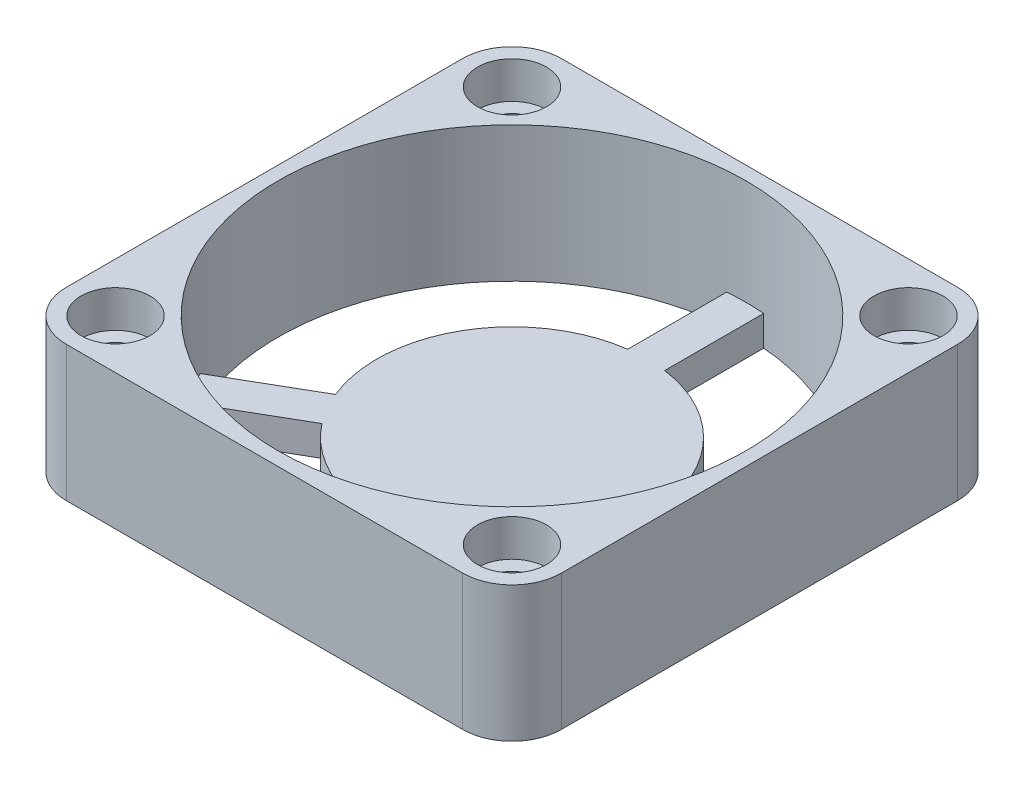
SolidWorks part; units mm, degrees
ref_plane "Plano frontal" through (0, 0, 0) normal (0, 0, 1) x (1, 0, 0)
ref_plane "Plano superior" through (0, 0, 0) normal (0, 1, 0) x (1, 0, 0)
ref_plane "Plano direito" through (0, 0, 0) normal (1, 0, 0) x (0, 0, -1)
sketch "Esboço1" plane through (0, 0, 0) normal (0, 1, 0) x (1, 0, 0)
  line L1 (-16.1, -20.1) -> (16.1, -20.1)
  line L2 (-20.1, -16.1) -> (-20.1, 16.1)
  line L3 (-16.1, 20.1) -> (16.1, 20.1)
  line L4 (20.1, -16.1) -> (20.1, 16.1)
  line L5 (0, 20.1) -> (0, -20.1) construction
  line L6 (-20.1, 0) -> (20.1, 0) construction
  arc A0 (16.1, -20.1) -> (20.1, -16.1) centre (16.1, -16.1) ccw
  arc A1 (-20.1, 16.1) -> (-16.1, 20.1) centre (-16.1, 16.1) cw
  arc A2 (-16.1, -20.1) -> (-20.1, -16.1) centre (-16.1, -16.1) cw
  arc A3 (16.1, 20.1) -> (20.1, 16.1) centre (16.1, 16.1) cw
  point P0 (0, 0)
  dimension "D1" = 4
  dimension "D2" = 40.2
  dimension "D3" = 40.2
extrude "Ressalto-extrusão1" add sketch "Esboço1" along normal mid plane 11
sketch "Esboço2" plane through (0, 5.5, 0) normal (0, 1, 0) x (1, 0, 0)
  line L1 (20.1, -16.1) -> (20.1, 16.1) construction
  circle A0 centre (0, 0) radius 19
  dimension "D1" = 1.1
extrude "Corte-extrusão1" cut sketch "Esboço2" against normal blind 8.55
sketch "Esboço3" plane through (0, -3.05, 0) normal (0, 1, 0) x (1, 0, 0)
  line L1 (1.5, 10.8972) -> (1.5, 18.9407)
  line L2 (-1.5, 10.8972) -> (-1.5, 18.9407)
  line L4 (8.6873, -6.7477) -> (15.6531, -10.7694)
  line L5 (10.1873, -4.1496) -> (17.1531, -8.1713)
  line L7 (-10.1873, -4.1496) -> (-17.1531, -8.1713)
  line L8 (-8.6873, -6.7477) -> (-15.6531, -10.7694)
  arc A0 (-8.6873, -6.7477) -> (8.6873, -6.7477) centre (0, 0) ccw
  circle A1 centre (0, 0) radius 19
  arc A2 (-15.6531, -10.7694) -> (15.6531, -10.7694) centre (0, 0) ccw
  arc A3 (10.1873, -4.1496) -> (1.5, 10.8972) centre (0, 0) ccw
  arc A4 (17.1531, -8.1713) -> (1.5, 18.9407) centre (0, 0) ccw
  arc A5 (-1.5, 10.8972) -> (-10.1873, -4.1496) centre (0, 0) ccw
  arc A6 (-1.5, 18.9407) -> (-17.1531, -8.1713) centre (0, 0) ccw
  point P25 (0, 0)
  dimension "D2" = 22
  dimension "D1" = 0
  dimension "D5" = 3
extrude "Corte-extrusão2" cut sketch "Esboço3" against normal through all
sketch "Esboço4" plane through (0, -5.5, 0) normal (0, -1, 0) x (1, 0, 0)
  line L0 (0, -6.05) -> (0, 6.05) construction
  line L1 (6.05, 0) -> (-6.05, 0) construction
  circle A0 centre (-16.1, 16.1) radius 1.6
  circle A1 centre (16.1, 16.1) radius 1.6
  circle A2 centre (16.1, -16.1) radius 1.6
  circle A3 centre (-16.1, -16.1) radius 1.6
  dimension "D1" = 3.2
extrude "Corte-extrusão3" cut sketch "Esboço4" against normal through all
sketch "Esboço5" plane through (0, 5.5, 0) normal (0, 1, 0) x (1, 0, 0)
  line L0 (-6.05, 0) -> (6.05, 0) construction
  line L1 (0, -6.05) -> (0, 6.05) construction
  circle A0 centre (-16.1, 16.1) radius 2.8
  circle A1 centre (-16.1, -16.1) radius 2.8
  circle A2 centre (16.1, -16.1) radius 2.8
  circle A3 centre (16.1, 16.1) radius 2.8
  dimension "D1" = 5.6
extrude "Corte-extrusão4" cut sketch "Esboço5" against normal blind 3
